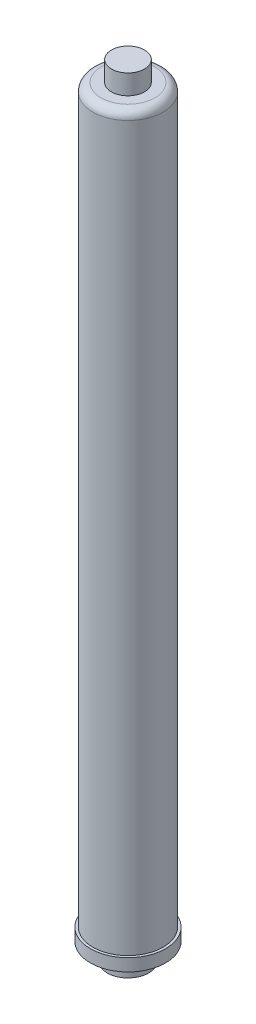
SolidWorks part; units mm, degrees
ref_plane "Front Plane" through (0, 0, 0) normal (0, 0, 1) x (1, 0, 0)
ref_plane "Top Plane" through (0, 0, 0) normal (0, 1, 0) x (1, 0, 0)
ref_plane "Right Plane" through (0, 0, 0) normal (1, 0, 0) x (0, 0, -1)
sketch "Sketch1" plane through (0, 0, 0) normal (0, 0, 1) x (1, 0, 0)
  line L0 (14.605, -22.733) -> (15.875, -22.733)
  line L1 (15.875, -22.733) -> (15.875, -9.525)
  line L2 (15.875, -9.525) -> (28.8925, -9.525)
  line L3 (28.8925, -9.525) -> (28.8925, 0)
  line L4 (28.8925, 0) -> (26.9875, 0)
  line L5 (26.9875, 0) -> (26.9875, 556.006)
  line L6 (20.6375, 562.356) -> (12.7, 562.356)
  line L7 (12.7, 562.356) -> (12.7, 577.596)
  line L8 (12.7, 577.596) -> (0, 577.596)
  line L9 (0, 577.596) -> (0, 28.067)
  line L10 (0, 28.067) -> (14.605, -22.733)
  arc A0 (26.9875, 556.006) -> (20.6375, 562.356) centre (20.6375, 556.006) ccw
  point P10 (0, -21.9805)
  point P15 (17.0934, -23.6238)
  point P16 (9.9323, -20.1465)
  point P17 (0, 0)
  point P18 (0, 0)
  point P19 (5.5292, -22.9196)
  dimension "D4" = 6.35
  dimension "D1" = 9.525
  dimension "D2" = 562.356
  dimension "D3" = 15.24
  dimension "D5" = 15.875
  dimension "D6" = 26.9875
  dimension "D7" = 28.8925
  dimension "D8" = 1.27
  dimension "D9" = 50.8
  dimension "D10" = 13.208
  dimension "D11" = 12.7
revolve "Revolve1" add sketch "Sketch1" angle 360 about L9
